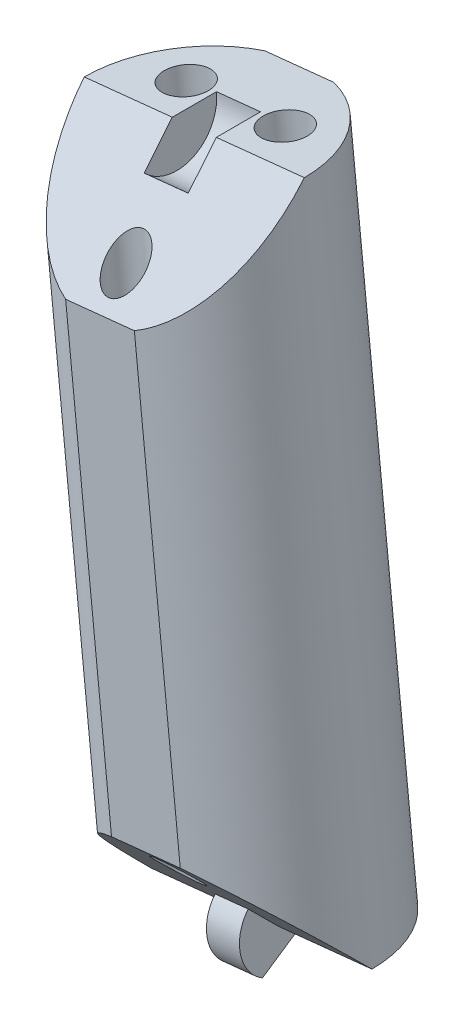
SolidWorks part; units mm, degrees
ref_plane "Front Plane" through (0, 0, 0) normal (0, 0, 1) x (1, 0, 0)
ref_plane "Top Plane" through (0, 0, 0) normal (0, 1, 0) x (1, 0, 0)
ref_plane "Right Plane" through (0, 0, 0) normal (1, 0, 0) x (0, 0, -1)
sketch "Sketch2" plane through (0, 0, 0) normal (0, 0, 1) x (1, 0, 0)
  line L0 (0, 0) -> (90, 0)
  line L1 (90, 0) -> (90, 120)
  line L2 (90, 120) -> (0, 120)
  line L3 (0, 120) -> (0, 0)
  line L4 (0, 120) -> (-10, 120)
  line L5 (-10, 120) -> (-10, 16.9491)
  line L6 (-10, 120) -> (57.5, 127)
  line L7 (57.5, 127) -> (90, 124)
  line L8 (90, 120) -> (99, 60)
  line L10 (90, 124) -> (90, 120)
  line L11 (5.9147, 0) -> (5.9147, -25)
  line L12 (5.9147, -25) -> (-4.0853, -25)
  line L13 (-4.0853, -29) -> (-4.0853, 0)
  line L14 (80, 0) -> (80, -25)
  line L15 (80, -25) -> (90, -25)
  line L16 (90, -29) -> (90, 0)
  line L17 (15.7927, 122.6748) -> (5.4776, 222.1414)
  line L18 (5.4776, 222.1414) -> (21.3923, 223.7918)
  line L19 (21.3923, 223.7918) -> (31.7073, 124.3252)
  line L20 (7.6492, 201.201) -> (23.5639, 202.8514)
  line L21 (10.9066, 169.7905) -> (26.8212, 171.441)
  line L22 (-10, 120) -> (-20.0396, 216.8108)
  line L23 (-20.0396, 216.8108) -> (-4.125, 218.4612)
  line L24 (-4.125, 218.4612) -> (5.9147, 121.6504)
  line L25 (-17.926, 196.4296) -> (-2.0114, 198.08)
  line L26 (-14.7556, 165.8578) -> (1.159, 167.5082)
  line L27 (57.5, 127) -> (46.9095, 229.1223)
  line L28 (46.9095, 229.1223) -> (30.9949, 227.4719)
  line L29 (30.9949, 227.4719) -> (41.5853, 125.3496)
  line L30 (33.2245, 205.9725) -> (49.1391, 207.6229)
  line L31 (36.5688, 173.7233) -> (52.4835, 175.3737)
  line L34 (90, 124) -> (99.1917, 223.5767)
  line L35 (99.1917, 223.5767) -> (83.2594, 225.0473)
  line L36 (83.2594, 225.0473) -> (74.0677, 125.4707)
  line L38 (81.3243, 204.0838) -> (97.2566, 202.6132)
  line L39 (78.4217, 172.6386) -> (94.354, 171.1679)
  line L40 (62.4078, 79.6749) -> (57.5, 127) construction
  line L41 (41.5853, 125.3496) -> (46.4931, 78.0244) construction
  line L42 (46.4931, 78.0244) -> (62.4078, 79.6749) construction
  line L43 (31.7073, 124.3252) -> (36.6151, 77.0001) construction
  line L44 (36.6151, 77.0001) -> (20.7005, 75.3496) construction
  line L45 (20.7005, 75.3496) -> (15.7927, 122.6748) construction
  line L46 (5.9147, 121.6504) -> (10.8224, 74.3253) construction
  line L47 (10.8224, 74.3253) -> (-5.0922, 72.6749) construction
  line L48 (-5.0922, 72.6749) -> (-10, 120) construction
  line L49 (74.0677, 125.4707) -> (69.6944, 78.0931) construction
  line L50 (69.6944, 78.0931) -> (85.7624, 78.0931) construction
  line L51 (85.7624, 78.0931) -> (90, 124) construction
  line L52 (-12.0823, 217.636) -> (10.4873, 0) construction
  line L53 (13.4349, 222.9666) -> (36.5574, 0) construction
  line L54 (38.9522, 228.2971) -> (62.6275, 0) construction
  line L55 (91.2256, 224.312) -> (70.5198, 0) construction
  line L59 (99, 60) -> (93.5277, 44.9649)
  line L60 (99, 60) -> (169.4769, 34.3485)
  line L61 (169.4769, 34.3485) -> (164.0046, 19.3134)
  line L62 (164.0046, 19.3134) -> (93.5277, 44.9649)
  line L63 (90, -2) -> (100, -2)
  line L64 (141.2862, 44.6091) -> (135.8138, 29.574)
  line L65 (99, 60) -> (55.7741, 75.7329) construction
  line L66 (55.7741, 75.7329) -> (50.3018, 60.6978) construction
  line L67 (100, -2) -> (100, -29)
  line L70 (-4.0853, -2) -> (-14.0853, -2)
  line L71 (-14.0853, -2) -> (-14.0853, -29)
  line L74 (-4.0853, 0) -> (0, 0)
  line L75 (-14.0853, -29) -> (-14.0853, -112.587)
  line L76 (-14.0853, -112.587) -> (100, -112.587)
  line L77 (100, -112.587) -> (100, -29)
  line L78 (-14.0853, -29) -> (100, -29)
  line L79 (-14.0853, -14.5) -> (100, -14.5) construction
  line L80 (31.7073, -112.587) -> (31.7073, -122.6232)
  line L81 (31.7073, -122.6232) -> (42.9573, -122.6232)
  line L82 (42.9573, -122.6232) -> (42.9573, -112.587)
  line L83 (-14.0853, -112.587) -> (-88.3667, -112.587)
  line L84 (-88.3667, -112.587) -> (-88.3667, -128.2699)
  line L85 (-88.3667, -128.2699) -> (169.4958, -128.2699)
  line L86 (169.4958, -128.2699) -> (169.4958, -112.587)
  line L87 (169.4958, -112.587) -> (100, -112.587)
  line L88 (90, 60) -> (-10, 60) construction
  line L89 (50.3018, 60.6978) -> (93.5277, 44.9649) construction
  line L90 (87.2806, 55.7521) -> (166.7408, 26.8309) construction
  line L91 (87.2806, 55.7521) -> (82.1749, 52.5336) construction
  line L92 (82.1749, 52.5336) -> (77.3257, 0) construction
  line L93 (83.1185, 56.6957) -> (86.337, 51.59) construction
  arc A0 (-10, 16.9491) -> (-4.0853, 0) centre (14.9876, 16.1624) ccw
  arc A1 (93.5277, 44.9649) -> (90, 0) centre (-126.4069, 39.5988) cw
  point P42 (41.1818, 206.7977)
  point P100 (84.7278, 54.1428)
  point P101 (84.7278, 54.1428)
  dimension "D11" = 47.3684
  dimension "D35" = 9
  dimension "D32" = 220
  dimension "D36" = 25
  dimension "D1" = 120
  dimension "D2" = 90
  dimension "D3" = 10
  dimension "D5" = 67.862
  dimension "D6" = 7
  dimension "D7" = 4
  dimension "D8" = 16
  dimension "D9" = 16
  dimension "D10" = 100
  dimension "D12" = 31.5789
  dimension "D13" = 16
  dimension "D14" = 16
  dimension "D15" = 16
  dimension "D16" = 25.7927
  dimension "D17" = 100
  dimension "D18" = 21.0526
  dimension "D19" = 31.5789
  dimension "D20" = 97.33
  dimension "D21" = 102.67
  dimension "D22" = 20.4905
  dimension "D23" = 30.7358
  dimension "D24" = 21.6147
  dimension "D25" = 32.4221
  dimension "D26" = 25
  dimension "D28" = 25
  dimension "D29" = 75
  dimension "D30" = 47.5789
  dimension "D31" = 30
  dimension "D33" = 46
  dimension "D34" = 20
  dimension "D37" = 2
  dimension "D38" = 2
  dimension "D39" = 27
  dimension "D40" = 10
  dimension "D41" = 10
  dimension "D42" = 27
  dimension "D43" = 14.5
  dimension "D44" = 127.5
ref_plane "Plane1" through (87.2806, 55.7521, 0) normal (-0.846, -0.5333, 0) x (0, 0, 1)
ref_plane "Plane2" through (82.1749, 52.5336, 0) normal (-0.0919, -0.9958, 0) x (-0.9958, 0.0919, 0)
ref_plane "Plane3" through (91.2256, 224.312, 0) normal (-0.0919, -0.9958, 0) x (-0.9958, 0.0919, 0)
ref_plane "Plane4" through (38.9522, 228.2971, 0) normal (0.1032, -0.9947, 0) x (-0.9947, -0.1032, 0)
ref_plane "Plane5" through (13.4349, 222.9666, 0) normal (0.1032, -0.9947, 0) x (-0.9947, -0.1032, 0)
ref_plane "Plane7" through (166.7408, 26.8309, 0) normal (0.9397, -0.342, 0) x (0, 0, -1)
ref_plane "Plane8" through (110.4217, -40.1902, 0) normal (0.9397, -0.342, 0) x (0, 0, -1)
ref_plane "Plane9" through (19.3664, 209.803, 0) normal (-0.0919, -0.9958, 0) x (-0.9958, 0.0919, 0)
ref_plane "Plane10" through (16.4638, 178.3578, 0) normal (-0.0919, -0.9958, 0) x (-0.9958, 0.0919, 0)
ref_plane "Plane11" through (-20.7793, 200.3721, 0) normal (0.1032, -0.9947, 0) x (-0.9947, -0.1032, 0)
ref_plane "Plane12" through (-17.435, 168.1229, 0) normal (0.1032, -0.9947, 0) x (-0.9947, -0.1032, 0)
ref_plane "Plane13" through (-20.5619, 198.2754, 0) normal (0.1032, -0.9947, 0) x (-0.9947, -0.1032, 0)
ref_plane "Plane14" through (-17.3045, 166.8649, 0) normal (0.1032, -0.9947, 0) x (-0.9947, -0.1032, 0)
ref_plane "Plane15" through (-12.0823, 217.636, 0) normal (0.1032, -0.9947, 0) x (-0.9947, -0.1032, 0)
ref_plane "Plane16" through (-20.3445, 196.1788, 0) normal (0.1032, -0.9947, 0) x (-0.9947, -0.1032, 0)
ref_plane "Plane17" through (-17.1741, 165.607, 0) normal (0.1032, -0.9947, 0) x (-0.9947, -0.1032, 0)
ref_plane "Plane18" through (12.1098, 131.1899, 0) normal (-0.0919, -0.9958, 0) x (-0.9958, 0.0919, 0)
ref_plane "Plane19" through (-12.4184, 119.7492, 0) normal (0.1032, -0.9947, 0) x (-0.9947, -0.1032, 0)
ref_plane "Plane20" through (0, 0, 0) normal (0, 0, 1) x (0.1032, -0.9947, 0)
ref_plane "Plane21" through (0, 0, 0) normal (0, 0, 1) x (-0.0919, -0.9958, 0)
ref_plane "Plane22" through (10.3758, 1.076, 0) normal (-0.9947, -0.1032, 0) x (0.1032, -0.9947, 0)
ref_plane "Plane23" through (36.1684, 3.7508, 0) normal (-0.9947, -0.1032, 0) x (0.1032, -0.9947, 0)
ref_plane "Plane24" through (61.9611, 6.4256, 0) normal (-0.9947, -0.1032, 0) x (0.1032, -0.9947, 0)
ref_plane "Plane25" through (69.924, -6.4545, 0) normal (-0.9958, 0.0919, 0) x (-0.0919, -0.9958, 0)
sketch "Sketch3" plane through (-20.3445, 196.1788, 0) normal (0.1032, -0.9947, 0) x (-0.9947, -0.1032, 0)
  line L0 (-2.4314, 0) -> (-18.4314, 0) construction
  circle A0 centre (-10.4314, 0) radius 8
  dimension "D1" = 16
extrude "Boss-Extrude1" add sketch "Sketch3" along normal blind 47.3684
sketch "Sketch4" plane through (10.3758, 1.076, 0) normal (-0.9947, -0.1032, 0) x (0.1032, -0.9947, 0)
  line L0 (-197.2309, 0) -> (-189.2309, 8)
  line L1 (-197.2309, 8) -> (-197.2309, -8) construction
  line L2 (-149.8624, 8) -> (-197.2309, 8) construction
  line L3 (-189.2309, 8) -> (-197.2309, 8)
  line L4 (-197.2309, 8) -> (-197.2309, 0)
  line L5 (-157.8624, 8) -> (-149.8624, 8)
  line L6 (-149.8624, 8) -> (-149.8624, 0)
  line L7 (-217.7214, 0) -> (1.0818, 0) construction
  line L8 (-149.8624, 0) -> (-157.8624, 8)
  dimension "D1" = 45
  dimension "D2" = 45
extrude "Cut-Extrude1" cut sketch "Sketch4" against normal through all and the other way through all
sketch "Sketch5" plane through (10.3758, 1.076, 0) normal (-0.9947, -0.1032, 0) x (0.1032, -0.9947, 0)
  line L1 (-149.8624, -2.8) -> (-147.4376, 1.4)
  line L6 (-149.8624, 0) -> (-157.8624, 8) construction
  line L11 (-149.8624, -8) -> (-149.8624, 0) construction
  line L12 (-151.8423, 1.9799) -> (-149.8624, 0)
  line L13 (-149.8624, 0) -> (-149.8624, -2.8)
  arc A3 (-151.8423, 1.9799) -> (-147.4376, 1.4) centre (-149.8624, 0) cw
  dimension "D2" = 2.8
  dimension "D1" = 30
  dimension "D3" = 2.8
extrude "Boss-Extrude2" add sketch "Sketch5" along normal mid plane 2.4
sketch "Sketch7" plane through (10.3758, 1.076, 0) normal (-0.9947, -0.1032, 0) x (0.1032, -0.9947, 0)
  line L6 (-197.2309, 0) -> (-197.2309, -8) construction
  line L7 (-189.2309, 8) -> (-197.2309, 0) construction
  line L8 (-194.9681, 2.2627) -> (-197.2309, 0)
  line L9 (-197.2309, 0) -> (-197.2309, -3.2)
  arc A1 (-197.2309, -3.2) -> (-194.9681, 2.2627) centre (-197.2309, 0) ccw
  dimension "D1" = 3.2
extrude "Cut-Extrude2" cut sketch "Sketch7" against normal mid plane 3.2
sketch "Sketch8" plane through (-20.3445, 196.1788, 0) normal (-0.1032, 0.9947, 0) x (0.9947, 0.1032, 0)
  line L0 (2.4314, 0) -> (18.4314, 0) construction
  circle A0 centre (10.4314, -5.5) radius 1.4
  circle A1 centre (6.8314, 3) radius 1.6
  circle A2 centre (14.0314, 3) radius 1.6
  point P9 (10.4314, 0)
  dimension "D1" = 3.2
  dimension "D2" = 3.2
  dimension "D3" = 2.8
  dimension "D4" = 3
  dimension "D5" = 5.5
  dimension "D6" = 3.6
  dimension "D7" = 3.6
  dimension "D8" = 3
extrude "Cut-Extrude3" cut sketch "Sketch8" against normal through all and the other way through all
sketch "Sketch9" plane through (-20.3445, 196.1788, 0) normal (-0.1032, 0.9947, 0) x (0.9947, 0.1032, 0)
  line L0 (7.9334, 7.6) -> (12.9294, 7.6)
  line L1 (-101.1265, 0) -> (155.3606, 0) construction
  line L2 (7.9334, -7.6) -> (12.9294, -7.6)
  arc A0 (18.4314, 0) -> (2.4314, 0) centre (10.4314, 0) ccw construction
  arc A1 (7.9334, 7.6) -> (12.9294, 7.6) centre (10.4314, 0) cw
  arc A2 (2.4314, 0) -> (18.4314, 0) centre (10.4314, 0) ccw construction
  arc A3 (7.9334, -7.6) -> (12.9294, -7.6) centre (10.4314, 0) ccw
  dimension "D1" = 7.6
  dimension "D2" = 7.6
extrude "Cut-Extrude4" cut sketch "Sketch9" against normal through all
